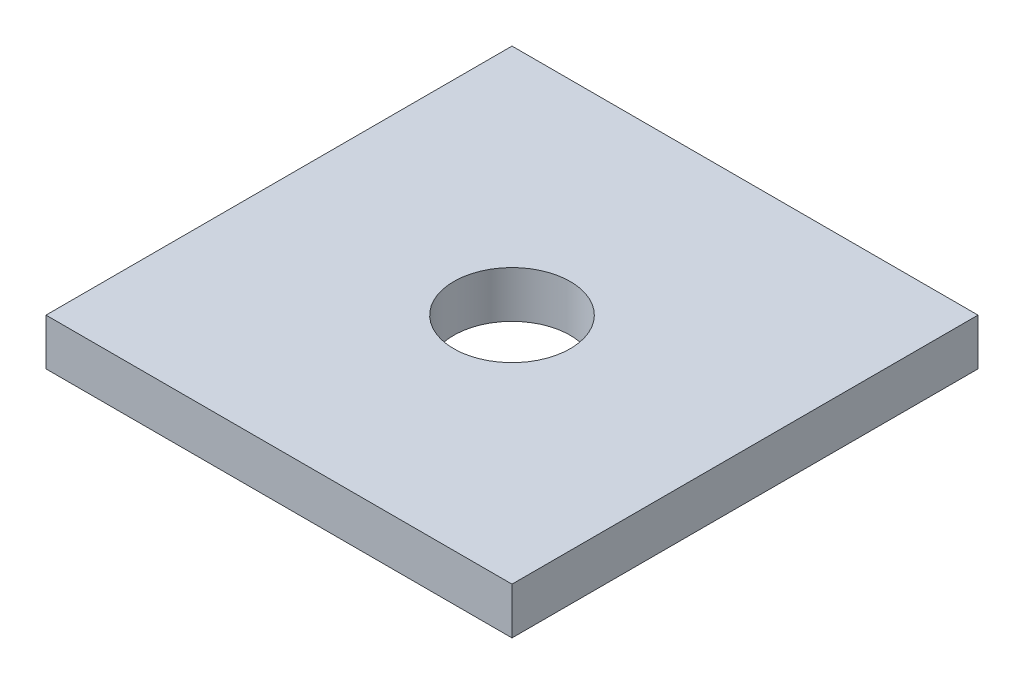
SolidWorks part; units mm, degrees
ref_plane "Front Plane" through (0, 0, 0) normal (0, 0, 1) x (1, 0, 0)
ref_plane "Top Plane" through (0, 0, 0) normal (0, 1, 0) x (1, 0, 0)
ref_plane "Right Plane" through (0, 0, 0) normal (1, 0, 0) x (0, 0, -1)
sketch "Sketch1" plane through (0, 0, 0) normal (0, 1, 0) x (1, 0, 0)
  line L1 (0, 0) -> (25.4, 0)
  line L2 (0, 0) -> (0, 25.4)
  line L3 (0, 25.4) -> (25.4, 25.4)
  line L4 (25.4, 0) -> (25.4, 25.4)
  dimension "D1" = 25.4
  dimension "D2" = 25.4
extrude "Boss-Extrude1" add sketch "Sketch1" along normal blind 2.54
sketch "Sketch2" plane through (0, 2.54, 0) normal (0, 1, 0) x (1, 0, 0)
  line L0 (0, 12.7) -> (25.4, 12.7) construction
  line L1 (0, 25.4) -> (0, 0) construction
  line L2 (25.4, 0) -> (25.4, 25.4) construction
  line L3 (12.7, 25.4) -> (12.7, 0) construction
  line L4 (25.4, 25.4) -> (0, 25.4) construction
  line L5 (0, 0) -> (25.4, 0) construction
  circle A0 centre (12.7, 12.7) radius 3.175
  dimension "D1" = 6.35
extrude "Cut-Extrude1" cut sketch "Sketch2" against normal blind 2.54
